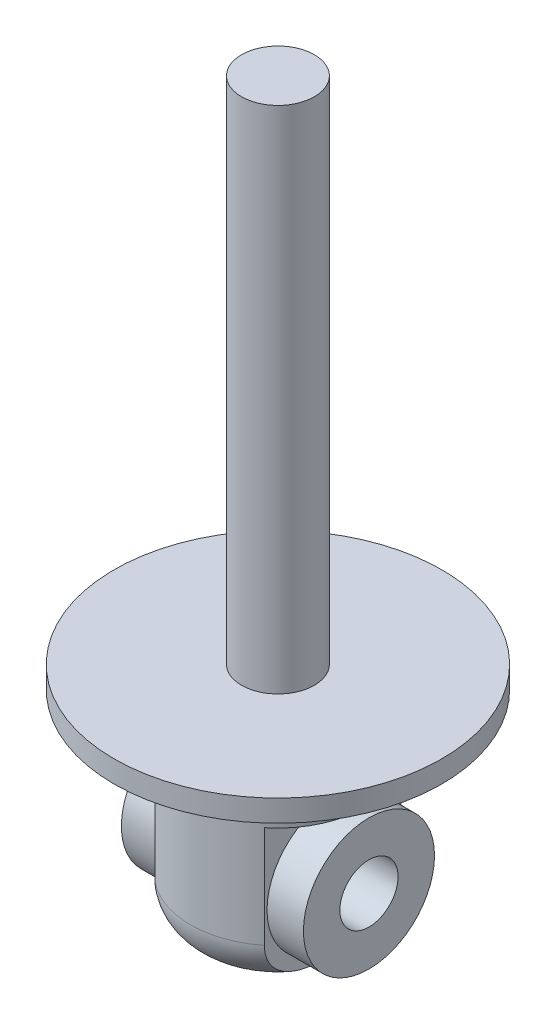
SolidWorks part; units mm, degrees
ref_plane "Front Plane" through (0, 0, 0) normal (0, 0, 1) x (1, 0, 0)
ref_plane "Top Plane" through (0, 0, 0) normal (0, 1, 0) x (1, 0, 0)
ref_plane "Right Plane" through (0, 0, 0) normal (1, 0, 0) x (0, 0, -1)
sketch "Sketch1" plane through (0, 0, 0) normal (0, 1, 0) x (1, 0, 0)
  circle A0 centre (0, 0) radius 22.5
  dimension "D1" = 45
extrude "Boss-Extrude1" add sketch "Sketch1" along normal blind 3
sketch "Sketch2" plane through (0, 3, 0) normal (0, 1, 0) x (1, 0, 0)
  circle A0 centre (0, 0) radius 5
  dimension "D1" = 10
extrude "Boss-Extrude2" add sketch "Sketch2" along normal blind 70
sketch "Sketch3" plane through (0, 0, 0) normal (0, -1, 0) x (1, 0, 0)
  circle A0 centre (0, 0) radius 12
  dimension "D1" = 24
extrude "Boss-Extrude3" add sketch "Sketch3" along normal blind 28
fillet "Fillet1" radius 6 1 edges at (0, -28, -12)
sketch "Sketch4" plane through (0, 0, 0) normal (0, 0, 1) x (1, 0, 0)
  line L0 (0, -28) -> (0, 0) construction
  line L1 (-6, -28) -> (6, -28) construction
  line L2 (-22.0227, -28) -> (-22.0227, -8)
  line L3 (7.5, -28) -> (22.0227, -28)
  line L4 (7.5, -28) -> (7.5, -8)
  line L5 (7.5, -8) -> (22.0227, -8)
  line L6 (22.0227, -28) -> (22.0227, -8)
  line L7 (-7.5, -8) -> (-22.0227, -8)
  line L8 (-7.5, -28) -> (-7.5, -8)
  line L9 (-7.5, -28) -> (-22.0227, -28)
  dimension "D1" = 20
  dimension "D2" = 15
extrude "Cut-Extrude2" cut sketch "Sketch4" against normal mid plane 28
sketch "Sketch5" plane through (7.5, 0, 0) normal (1, 0, 0) x (0, 0, -1)
  line L0 (0, 0) -> (0, -28) construction
  line L1 (-6, -28) -> (6, -28) construction
  circle A0 centre (0, -18) radius 4
  dimension "D1" = 8
  dimension "D2" = 10
extrude "Cut-Extrude3" cut sketch "Sketch5" against normal through all
sketch "Sketch6" plane through (7.5, 0, 0) normal (1, 0, 0) x (0, 0, -1)
  circle A1 centre (0, -18) radius 4 construction
  circle A2 centre (0, -18) radius 4
sketch "Sketch7" plane through (0, 0, 0) normal (1, 0, 0) x (0, 0, -1)
  circle A0 centre (0, -18) radius 9
  circle A1 centre (0, -18) radius 4 construction
  circle A2 centre (0, -18) radius 4
  dimension "D1" = 18
extrude "Boss-Extrude4" add sketch "Sketch7" along normal mid plane 25
